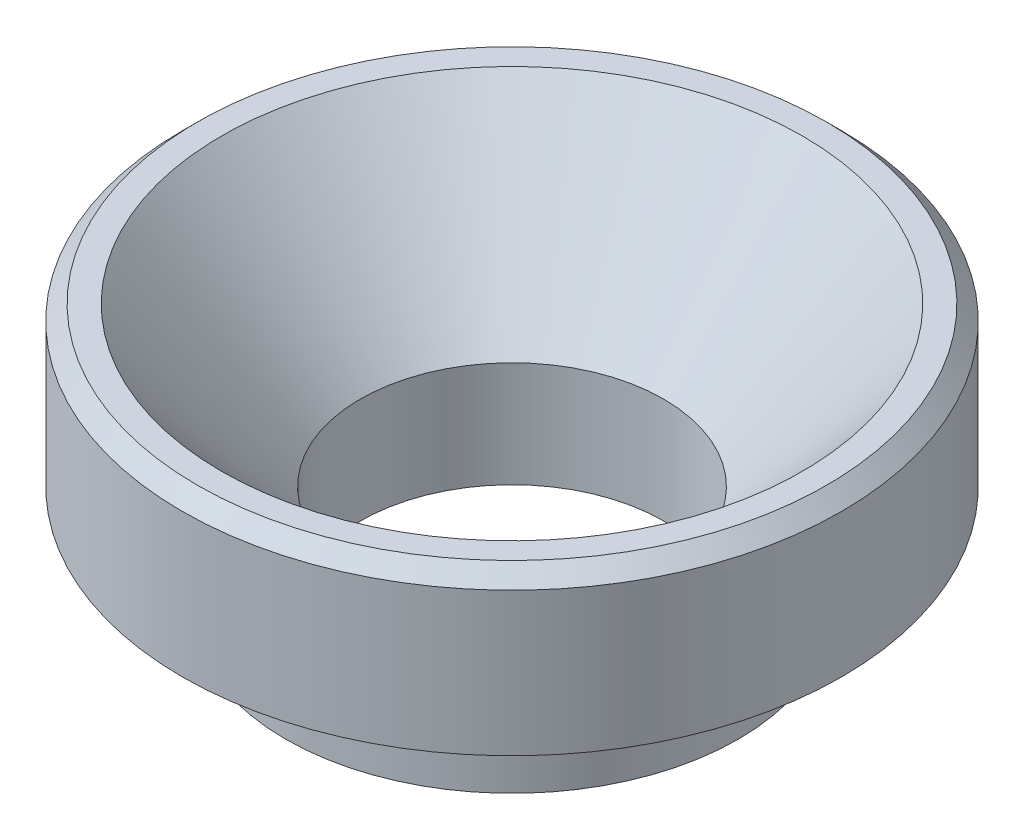
SolidWorks part; units mm, degrees
ref_plane "Front Plane" through (0, 0, 0) normal (0, 0, 1) x (1, 0, 0)
ref_plane "Top Plane" through (0, 0, 0) normal (0, 1, 0) x (1, 0, 0)
ref_plane "Right Plane" through (0, 0, 0) normal (1, 0, 0) x (0, 0, -1)
sketch "Sketch1" plane through (0, 0, 0) normal (0, 0, 1) x (1, 0, 0)
  line L0 (0, 0) -> (0, 82.5749) construction
  line L1 (2.5527, 0) -> (2.5527, 1.778)
  line L2 (2.5527, 1.778) -> (4.8895, 4.445)
  line L3 (4.8895, 4.445) -> (5.5499, 4.445)
  line L4 (5.5499, 4.445) -> (5.5499, 1.778)
  line L5 (5.5499, 1.778) -> (3.81, 1.778)
  line L6 (3.81, 1.778) -> (3.81, 0)
  line L7 (3.81, 0) -> (2.5527, 0)
  dimension "D1" = 5.1054
  dimension "D2" = 7.62
  dimension "D3" = 1.778
  dimension "D4" = 2.667
  dimension "D5" = 9.779
  dimension "D6" = 11.0998
revolve "Revolve1" add sketch "Sketch1" angle 360 about L0
chamfer "Chamfer1" distance 0.254 angle 45 1 edges at (0, 4.445, -5.5499)
fillet "Fillet1" radius 0.127 1 edges at (0, 1.778, -3.81)
